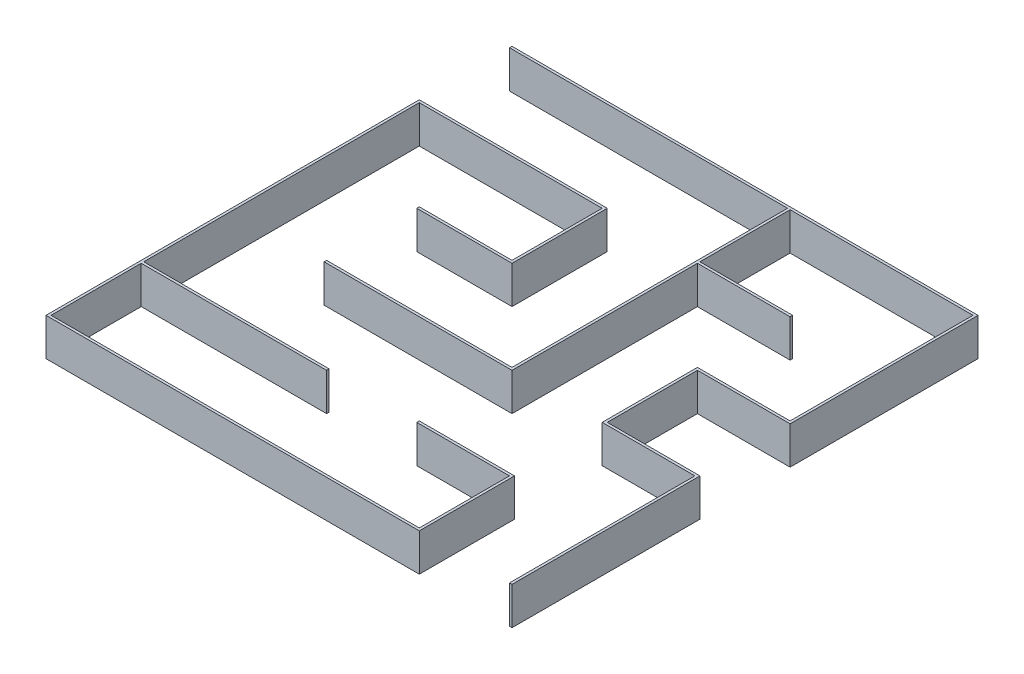
SolidWorks part; units mm, degrees
ref_plane "Front Plane" through (0, 0, 0) normal (0, 0, 1) x (1, 0, 0)
ref_plane "Top Plane" through (0, 0, 0) normal (0, 1, 0) x (1, 0, 0)
ref_plane "Right Plane" through (0, 0, 0) normal (1, 0, 0) x (0, 0, -1)
sketch "Sketch1" plane through (0, 0, 0) normal (0, 1, 0) x (1, 0, 0)
  line L2 (0, 1860) -> (-1860, 1860)
  line L4 (-1860, 1860) -> (-1860, 1850)
  line L5 (-10, 0) -> (0, 0)
  line L6 (-750, 370) -> (-380, 370)
  line L7 (-380, 370) -> (-380, 10)
  line L8 (-380, 10) -> (-1850, 10)
  line L9 (-1850, 10) -> (-1850, 370)
  line L10 (-1850, 370) -> (-1110, 370)
  line L11 (-1110, 370) -> (-1110, 380)
  line L12 (-1110, 380) -> (-1850, 380)
  line L13 (-1850, 380) -> (-1850, 1480)
  line L14 (-1850, 1480) -> (-1120, 1480)
  line L15 (-1120, 1480) -> (-1120, 1120)
  line L16 (-1120, 1120) -> (-1490, 1120)
  line L17 (-1490, 1120) -> (-1490, 1110)
  line L18 (-1490, 1110) -> (-1110, 1110)
  line L19 (-1110, 1110) -> (-1110, 1490)
  line L20 (-1110, 1490) -> (-1860, 1490)
  line L21 (-1860, 1490) -> (-1860, 0)
  line L22 (-1860, 0) -> (-370, 0)
  line L23 (-370, 0) -> (-370, 380)
  line L24 (-370, 380) -> (-750, 380)
  line L25 (-750, 380) -> (-750, 370)
  line L26 (-750, 1850) -> (-750, 750)
  line L27 (-750, 750) -> (-1490, 750)
  line L28 (-1490, 740) -> (-740, 740)
  line L29 (-740, 740) -> (-740, 1480)
  line L30 (-740, 1480) -> (-370, 1480)
  line L31 (-370, 1480) -> (-370, 1490)
  line L32 (-370, 1490) -> (-740, 1490)
  line L33 (-740, 1490) -> (-740, 1850)
  line L34 (-1490, 750) -> (-1490, 740)
  line L35 (-1860, 1850) -> (-750, 1850)
  line L36 (-10, 1850) -> (-740, 1850)
  line L38 (-370, 1110) -> (-370, 750)
  line L39 (0, 750) -> (-370, 750)
  line L40 (-10, 1120) -> (-380, 1120)
  line L41 (-380, 1120) -> (-380, 740)
  line L42 (-380, 740) -> (-10, 740)
  line L43 (-10, 740) -> (-10, 0)
  line L44 (-10, 1850) -> (-10, 1120)
  line L46 (0, 0) -> (0, 750)
  line L48 (0, 1860) -> (0, 1110)
  line L50 (-370, 1110) -> (0, 1110)
  dimension "D1" = 1860
  dimension "D3" = 1860
  dimension "D4" = 10
  dimension "D5" = 10
  dimension "D6" = 10
  dimension "D7" = 10
  dimension "D8" = 10
  dimension "D9" = 1490
  dimension "D10" = 10
  dimension "D11" = 10
  dimension "D12" = 10
  dimension "D13" = 10
  dimension "D14" = 10
  dimension "D15" = 380
  dimension "D16" = 360
  dimension "D17" = 740
  dimension "D18" = 1100
  dimension "D19" = 750
  dimension "D20" = 370
  dimension "D21" = 380
  dimension "D22" = 10
  dimension "D23" = 360
  dimension "D24" = 10
  dimension "D25" = 10
  dimension "D26" = 370
  dimension "D27" = 10
  dimension "D28" = 10
  dimension "D29" = 740
  dimension "D30" = 360
  dimension "D31" = 360
  dimension "D32" = 10
  dimension "D33" = 370
  dimension "D34" = 750
  dimension "D35" = 10
  dimension "D36" = 730
  dimension "D37" = 10
extrude "Boss-Extrude1" add sketch "Sketch1" along normal blind 150
